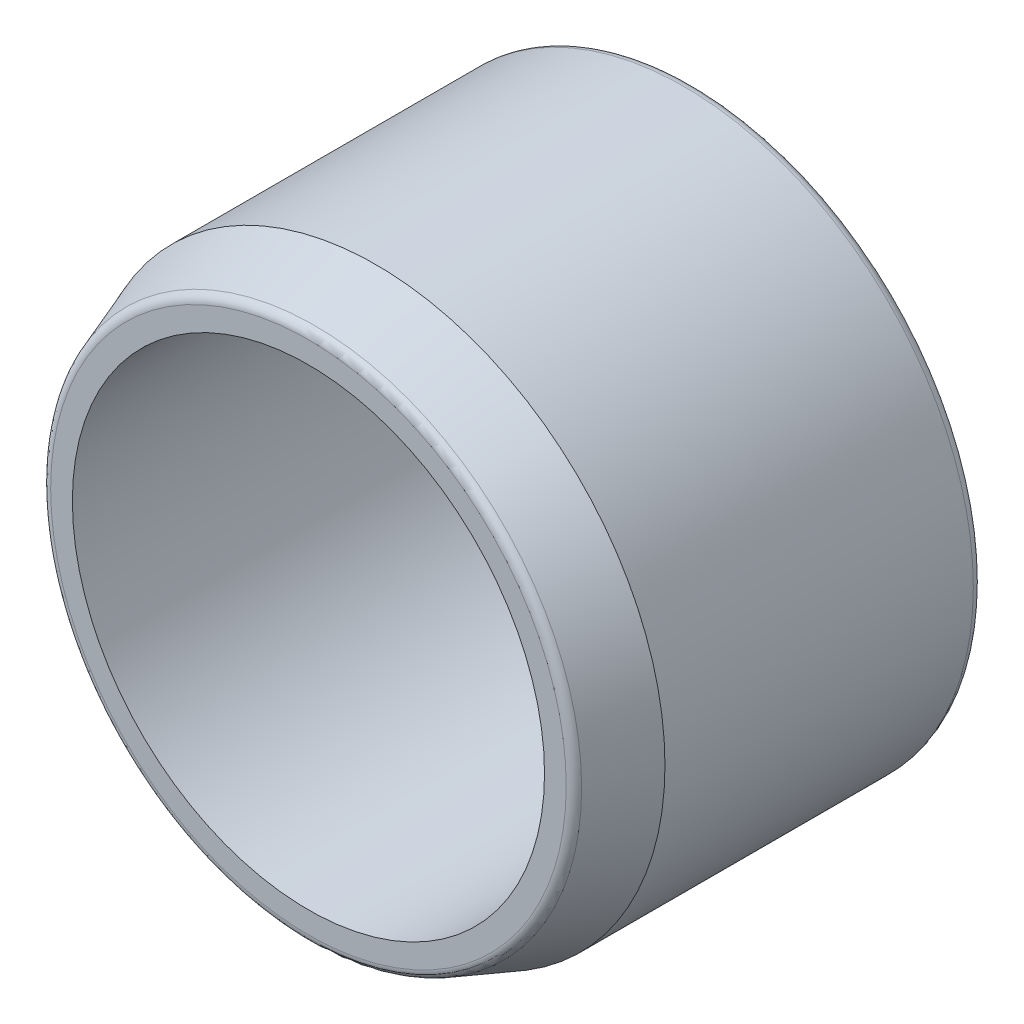
SolidWorks part; units mm, degrees
ref_plane "Front Plane" through (0, 0, 0) normal (0, 0, 1) x (1, 0, 0)
ref_plane "Top Plane" through (0, 0, 0) normal (0, 1, 0) x (1, 0, 0)
ref_plane "Right Plane" through (0, 0, 0) normal (1, 0, 0) x (0, 0, -1)
sketch "Sketch1" plane through (0, 0, 0) normal (0, 0, 1) x (1, 0, 0)
  circle A0 centre (0, 0) radius 30
  circle A1 centre (0, 0) radius 24.5
  dimension "D1" = 60
  dimension "D2" = 49
extrude "Boss-Extrude1" add sketch "Sketch1" along normal blind 40
chamfer "Chamfer1" distance 7 angle 20 1 edges at (30, 0, 40)
fillet "Fillet1" radius 1 2 edges at (30, 0, 0) (27.4522, 0, 40)
